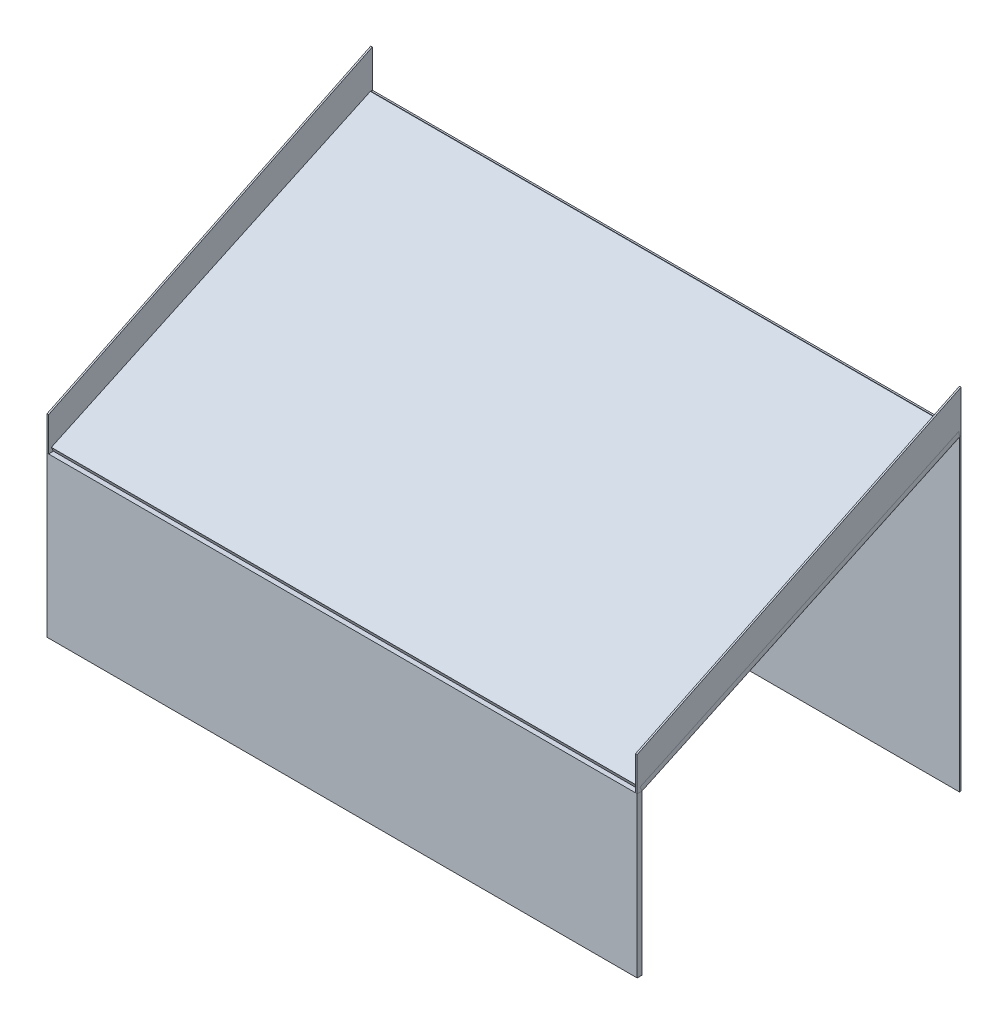
SolidWorks part; units mm, degrees
ref_plane "Front Plane" through (0, 0, 0) normal (0, 0, 1) x (1, 0, 0)
ref_plane "Top Plane" through (0, 0, 0) normal (0, 1, 0) x (1, 0, 0)
ref_plane "Right Plane" through (0, 0, 0) normal (1, 0, 0) x (0, 0, -1)
sketch "Sketch1" plane through (0, 0, 0) normal (0, 1, 0) x (1, 0, 0)
  line L0 (-182, 100) -> (-182, -100)
  line L1 (-185, 100) -> (185, 100)
  line L2 (-185, 100) -> (-185, -100)
  line L3 (-185, -100) -> (185, -100)
  line L4 (185, 100) -> (185, -100)
  line L5 (-185, 100) -> (185, -100) construction
  line L6 (-185, -100) -> (185, 100) construction
  line L7 (182, 100) -> (182, -100)
  line L8 (-182, 0) -> (-185, 0) construction
  point P0 (0, 0)
  dimension "D1" = 370
  dimension "D2" = 200
  dimension "D3" = 3
  dimension "D4" = 3
extrude "Boss-Extrude1" add sketch "Sketch1" along normal blind 100 contours L2 L3 L0 L1 | L1 L7 L3 L4
sketch "Sketch2" plane through (185, 0, 0) normal (1, 0, 0) x (0, 0, -1)
  line L0 (-100, 100) -> (100, 100)
  line L1 (100, 100) -> (100, 193.2615)
  line L2 (100, 193.2615) -> (-100, 100)
  dimension "D1" = 25
extrude "Boss-Extrude2" add sketch "Sketch2" against normal blind 3
sketch "Sketch3" plane through (0, 0, 100) normal (0, 0, 1) x (1, 0, 0)
  line L1 (-185, 100) -> (185, 100)
  line L2 (-185, 100) -> (-185, 0)
  line L3 (-185, 0) -> (185, 0)
  line L4 (185, 100) -> (185, 0)
extrude "Boss-Extrude3" add sketch "Sketch3" along normal blind 3
sketch "Sketch4" plane through (-185, 0, 0) normal (-1, 0, 0) x (0, 0, 1)
  line L0 (-100, 100) -> (-100, 193.2615)
  line L1 (-100, 193.2615) -> (100, 100)
  line L2 (100, 100) -> (-100, 100)
extrude "Boss-Extrude4" add sketch "Sketch4" against normal blind 3
sketch "Sketch5" plane through (0, 120.4416, 56.1628) normal (0, 0.9063, 0.4226) x (1, 0, 0)
  line L1 (-185, 172.3066) -> (185, 172.3066)
  line L2 (-185, 172.3066) -> (-185, -48.369)
  line L3 (-185, -48.369) -> (185, -48.369)
  line L4 (185, 172.3066) -> (185, -48.369)
extrude "Boss-Extrude7" add sketch "Sketch5" along normal blind 3 separate body
sketch "Sketch6" plane through (185, 0, 0) normal (1, 0, 0) x (0, 0, -1)
  line L0 (-100, 100) -> (-100, -1.363)
  line L5 (-103, 0) -> (100, 0)
  line L6 (100, 0) -> (100, 193.2615)
  line L7 (100, 193.2615) -> (-100, 100)
  line L8 (-100, 100) -> (-103, 100)
  line L9 (-103, 100) -> (-103, 0)
  line L10 (-103, 0) -> (100, 0)
  line L11 (100, 0) -> (100, 193.2615)
  line L12 (100, 193.2615) -> (-100, 100)
  line M6 (-103, 0) -> (100, 0)
  line M7 (100, 0) -> (100, 193.2615)
  line M8 (100, 193.2615) -> (-100, 100)
  dimension "D1" = 0
extrude "Cut-Extrude2" cut sketch "Sketch6" against normal through all contours L0 M8 M6 M7
ref_plane "Plane1" through (0, 0, -100) normal (0, 0, -1) x (-1, 0, 0)
sketch "Sketch7" plane through (0, 0, -100) normal (0, 0, -1) x (-1, 0, 0)
  line L1 (-185, 195.9805) -> (185, 195.9805)
  line L2 (-185, 195.9805) -> (-185, 0)
  line L3 (-185, 0) -> (185, 0)
  line L4 (185, 195.9805) -> (185, 0)
extrude "Boss-Extrude8" add sketch "Sketch7" against normal blind 1
sketch "Sketch8" plane through (185, 0, 0) normal (1, 0, 0) x (0, 0, -1)
  line L0 (-103, 100) -> (-103, 121.3255)
  line L1 (-103, 121.3255) -> (100, 219.2538)
  line L2 (100, -124.049) -> (100, 124.049) construction
  line L3 (100, 219.2538) -> (100, 193.0846)
  line L4 (100, 195.9805) -> (100, 0) construction
  line L5 (100, 193.0846) -> (-100, 100)
  line L6 (-100, 100) -> (-103, 100)
extrude "Boss-Extrude10" add sketch "Sketch8" against normal blind 1 separate body
sketch "Sketch9" plane through (-185, 0, 0) normal (-1, 0, 0) x (0, 0, 1)
  line L0 (103, 100) -> (100, 100)
  line L1 (100, 100) -> (-100, 193.0846)
  line L2 (-100, 124.049) -> (-100, -124.049) construction
  line L3 (100, 100) -> (-100, 193.0846) construction
  line L4 (-100, 193.0846) -> (-100, 219.4739)
  line L5 (-100, 219.4739) -> (103, 121.3255)
  line L6 (103, 121.3255) -> (103, 100)
extrude "Boss-Extrude12" add sketch "Sketch9" against normal blind 1 separate body
